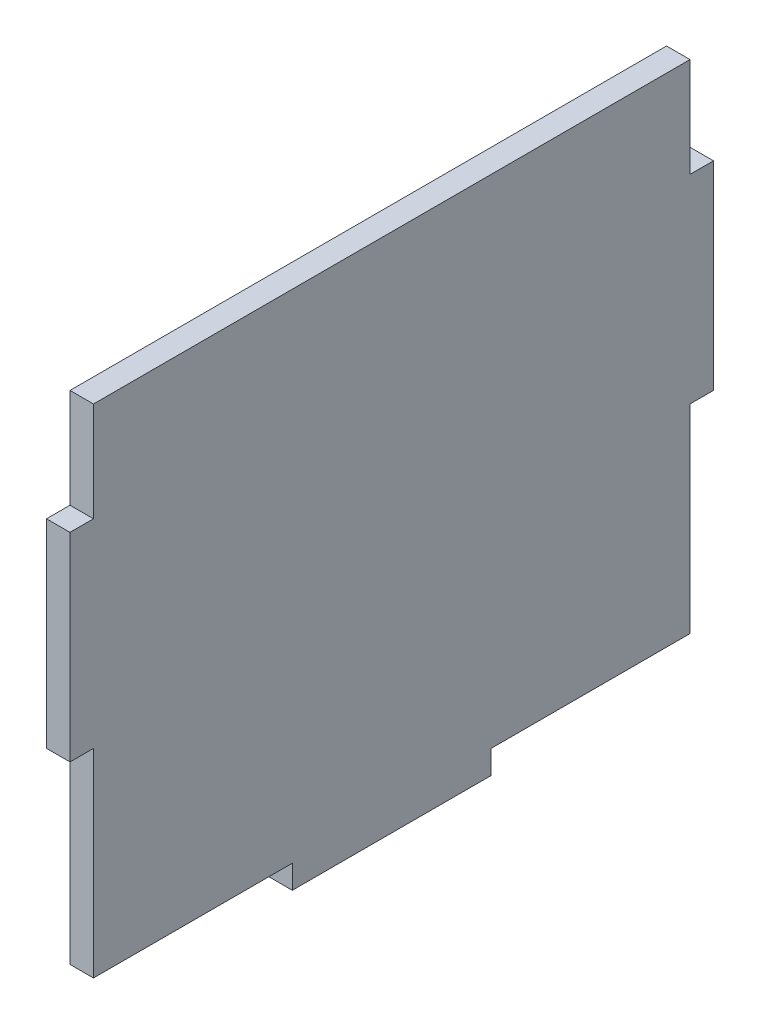
SolidWorks part; units mm, degrees
ref_plane "Front Plane" through (0, 0, 0) normal (0, 0, 1) x (1, 0, 0)
ref_plane "Top Plane" through (0, 0, 0) normal (0, 1, 0) x (1, 0, 0)
ref_plane "Right Plane" through (0, 0, 0) normal (1, 0, 0) x (0, 0, -1)
sketch "Sketch1" plane through (0, 0, 0) normal (1, 0, 0) x (0, 0, -1)
  line L0 (-38.1, -17.2847) -> (-38.1, -20.8153)
  line L1 (-38.1, 31.75) -> (38.1, 31.75)
  line L2 (-38.1, 31.75) -> (-38.1, 19.05)
  line L3 (-38.1, -31.75) -> (-12.7, -31.75)
  line L4 (38.1, 31.75) -> (38.1, 19.05)
  line L5 (0, -20.8153) -> (0, -42.0936) construction
  line L6 (38.1, -17.2847) -> (38.1, -20.8153)
  line L7 (12.7, -31.75) -> (38.1, -31.75)
  line L9 (-12.7, -31.75) -> (-12.7, -34.75)
  line L10 (-12.7, -34.75) -> (12.7, -34.75)
  line L11 (12.7, -31.75) -> (12.7, -34.75)
  line L16 (-38.1, -20.8153) -> (-38.1, -31.75)
  line L21 (-38.1, -6.35) -> (-38.1, -17.2847)
  line L23 (38.1, -6.35) -> (38.1, -17.2847)
  line L26 (-38.1, 19.05) -> (-41.1, 19.05)
  line L29 (-38.1, -6.35) -> (-41.1, -6.35)
  line L39 (38.1, -20.8153) -> (38.1, -31.75)
  line L40 (-41.1, 19.05) -> (-41.1, -6.35)
  line L41 (38.1, 19.05) -> (41.1, 19.05)
  line L43 (38.1, -6.35) -> (41.1, -6.35)
  line L44 (41.1, 19.05) -> (41.1, -6.35)
  dimension "D1" = 76.2
  dimension "D2" = 63.5
  dimension "D3" = 38.1
  dimension "D4" = 25.4
  dimension "D5" = 12.7
  dimension "D6" = 3
  dimension "D13" = 25.4
  dimension "D14" = 25.4
  dimension "D15" = 3
  dimension "D16" = 3
extrude "Boss-Extrude1" add sketch "Sketch1" along normal blind 3
